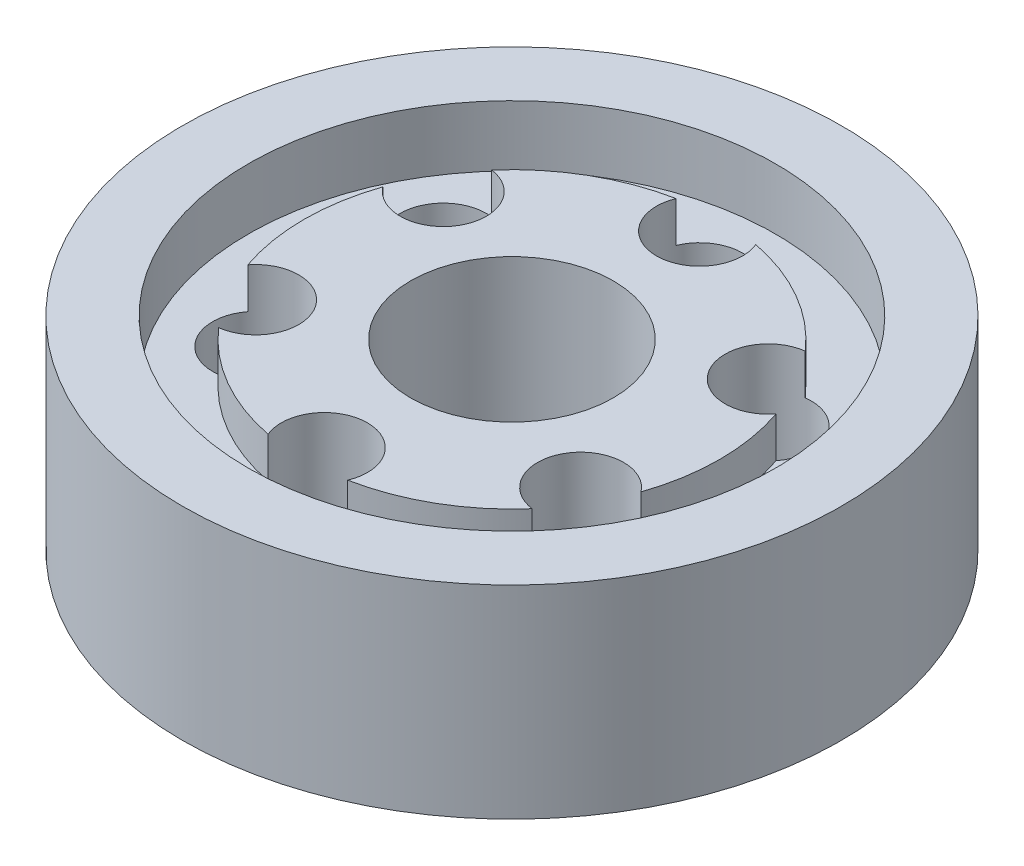
SolidWorks part; units mm, degrees
ref_plane "Front Plane" through (0, 0, 0) normal (0, 0, 1) x (1, 0, 0)
ref_plane "Top Plane" through (0, 0, 0) normal (0, 1, 0) x (1, 0, 0)
ref_plane "Right Plane" through (0, 0, 0) normal (1, 0, 0) x (0, 0, -1)
sketch "Sketch1" plane through (0, 0, 0) normal (0, 1, 0) x (1, 0, 0)
  circle A0 centre (0, 0) radius 32.5
  dimension "D1" = 65
extrude "Boss-Extrude1" add sketch "Sketch1" along normal blind 20
sketch "Sketch2" plane through (0, 20, 0) normal (0, 1, 0) x (1, 0, 0)
  circle A0 centre (0, 0) radius 26
  circle A1 centre (0, 0) radius 32.5 construction
  dimension "D1" = 6.5
extrude "Cut-Extrude1" cut sketch "Sketch2" against normal blind 6
sketch "Sketch3" plane through (0, 14, 0) normal (0, 1, 0) x (1, 0, 0)
  circle A0 centre (0, 0) radius 20.5
  dimension "D1" = 41
extrude "Boss-Extrude2" add sketch "Sketch3" along normal blind 4
hole_wizard "M10 Tapped Hole1" positions "Sketch7" profile "Sketch6" tap size "M10" standard "ISO"
sketch "Sketch7" plane through (0, 0, 0) normal (0, -1, 0) x (-1, 0, 0)
  circle A0 centre (0, 0) radius 32.5 construction
  point P0 (0, -18.5)
  dimension "D1" = 14
sketch "Sketch6" plane through (0, 0, 18.5) normal (1, 0, 0) x (0, 0, -1)
  line L0 (0, 0) -> (0, 37.0537)
  line L1 (0, 37.0537) -> (4.25, 34.5)
  line L2 (4.25, 34.5) -> (4.25, 0)
  line L5 (4.25, 0) -> (0, 0)
  line L10 (0, 37.0537) -> (-4.25, 34.5) construction
  line L11 (0, -6.35) -> (0, 107.95) construction
  dimension "Tap Drill Dia." = 8.5
  dimension "Tap Drill Depth" = 34.5
  dimension "Drill Angle" = 118
cosmetic thread "Hole Thread1" parameters "D1"=18, "D2"=10
sketch "Sketch8" plane through (0, 0, 0) normal (0, -1, 0) x (1, 0, 0)
  circle A0 centre (0, 0) radius 10
  dimension "D1" = 20
extrude "Cut-Extrude2" cut sketch "Sketch8" against normal through all
pattern_circular "CirPattern1" count 6 every 60 about axis through (0, 0, 0) along (0, 1, 0) of "M10 Tapped Hole1"
